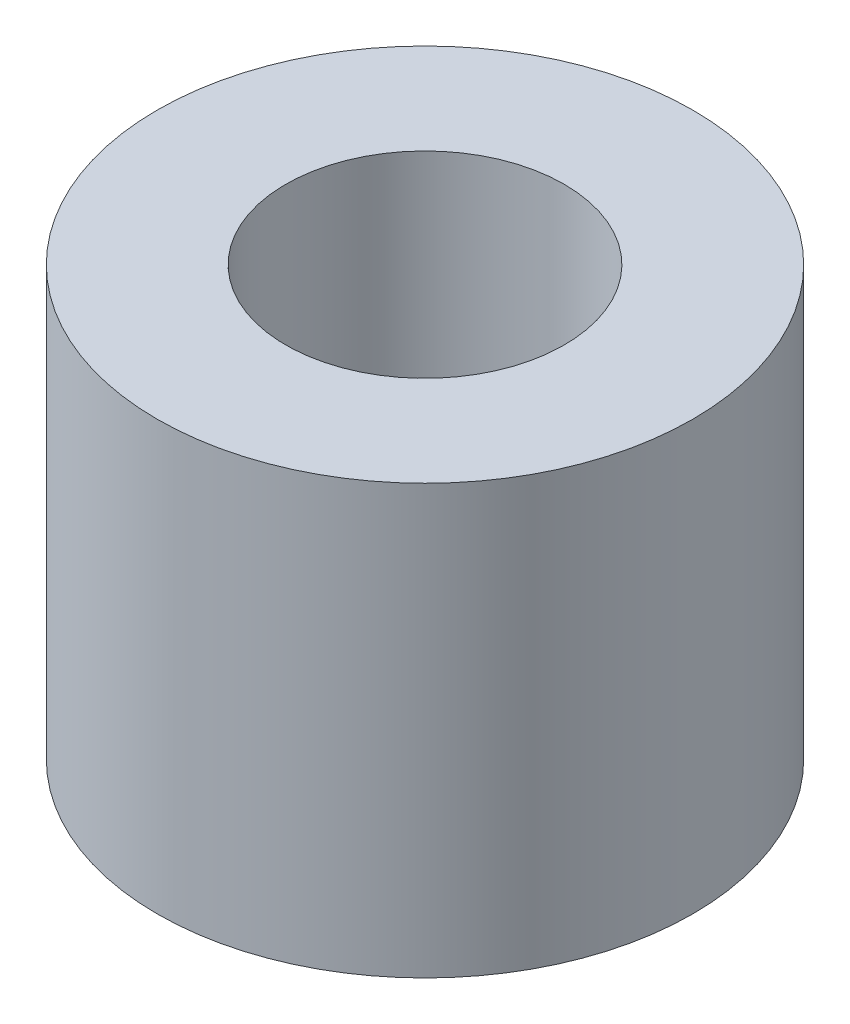
SolidWorks part; units mm, degrees
ref_plane "Front Plane" through (0, 0, 0) normal (0, 0, 1) x (1, 0, 0)
ref_plane "Top Plane" through (0, 0, 0) normal (0, 1, 0) x (1, 0, 0)
ref_plane "Right Plane" through (0, 0, 0) normal (1, 0, 0) x (0, 0, -1)
sketch "Sketch1" plane through (0, 0, 0) normal (0, 0, 1) x (1, 0, 0)
  line L0 (5, 8) -> (2.6, 8)
  line L1 (2.6, 8) -> (2.6, 0)
  line L2 (2.6, 0) -> (5, 0)
  line L3 (5, 0) -> (5, 8)
  line L4 (0, 8) -> (0, 0) construction
  dimension "D1" = 2.4
  dimension "D2" = 8
  dimension "D3" = 5
  dimension "D4" = 2.6
revolve "Revolve1" add sketch "Sketch1" angle 360 about L4
